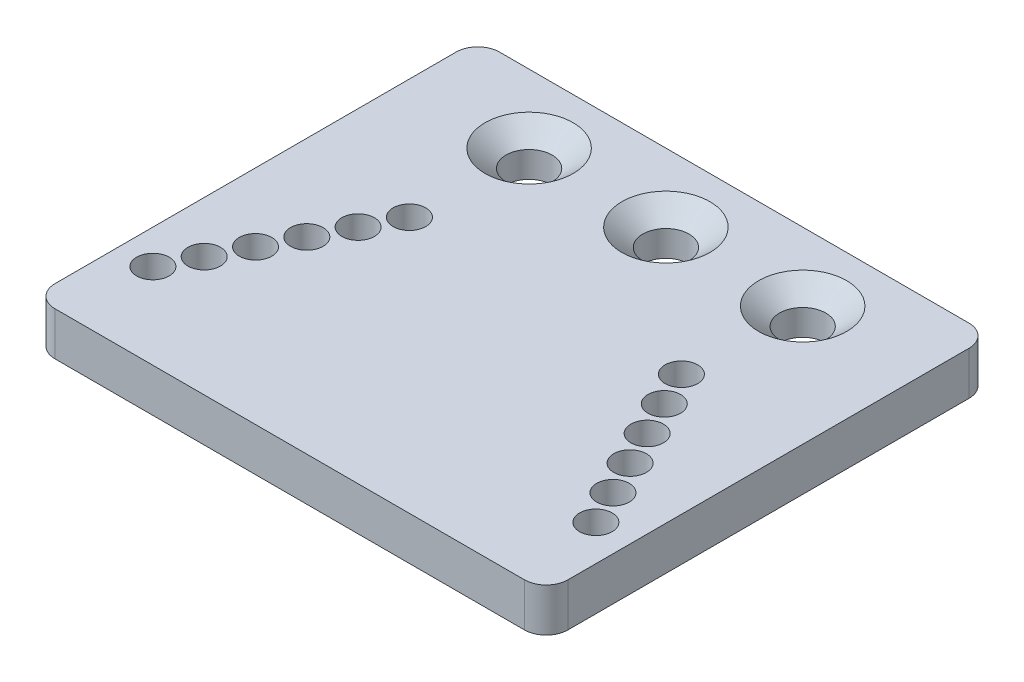
SolidWorks part; units mm, degrees
ref_plane "Front Plane" through (0, 0, 0) normal (0, 0, 1) x (1, 0, 0)
ref_plane "Top Plane" through (0, 0, 0) normal (0, 1, 0) x (1, 0, 0)
ref_plane "Right Plane" through (0, 0, 0) normal (1, 0, 0) x (0, 0, -1)
sketch "Sketch1" plane through (0, 0, 0) normal (0, 1, 0) x (1, 0, 0)
  line L1 (3.175, 0) -> (71.825, 0)
  line L2 (0, 3.175) -> (0, 61.825)
  line L3 (3.175, 65) -> (71.825, 65)
  line L4 (75, 3.175) -> (75, 61.825)
  line L5 (0, 0) -> (75, 65) construction
  line L6 (0, 65) -> (75, 0) construction
  arc A0 (75, 61.825) -> (71.825, 65) centre (71.825, 61.825) ccw
  arc A1 (75, 3.175) -> (71.825, 0) centre (71.825, 3.175) cw
  arc A2 (0, 3.175) -> (3.175, 0) centre (3.175, 3.175) ccw
  arc A3 (3.175, 65) -> (0, 61.825) centre (3.175, 61.825) ccw
  circle A4 centre (72.2625, 7.5) radius 2.3813 construction
  circle A5 centre (2.5, 7.5) radius 2.3813 construction
  circle A6 centre (5, 12.5) radius 2.3812
  circle A7 centre (69.7625, 12.5) radius 2.3813
  circle A8 centre (7.5, 17.5) radius 2.3813
  circle A9 centre (67.2625, 17.5) radius 2.3813
  circle A10 centre (10, 22.5) radius 2.3813
  circle A11 centre (64.7625, 22.5) radius 2.3813
  circle A12 centre (12.5, 27.5) radius 2.3813
  circle A13 centre (62.2625, 27.5) radius 2.3813
  circle A14 centre (15, 32.5) radius 2.3813
  circle A15 centre (59.7625, 32.5) radius 2.3812
  circle A16 centre (17.5, 37.5) radius 2.3813
  circle A17 centre (57.2625, 37.5) radius 2.3812
  circle A18 centre (37.5, 55) radius 3.3
  circle A19 centre (17.5, 55) radius 3.3
  circle A20 centre (57.5, 55) radius 3.3
  point P4 (37.5, 32.5)
  point P22 (69.8813, 7.5)
  point P23 (4.8813, 7.5)
  point P40 (9.8812, 17.5)
  point P41 (12.3812, 22.5)
  point P42 (14.8812, 27.5)
  point P43 (59.8812, 27.5)
  point P44 (7.3813, 12.5)
  point P45 (62.3813, 22.5)
  point P46 (64.8812, 17.5)
  point P47 (67.3813, 12.5)
  point P52 (17.3812, 32.5)
  point P53 (57.3812, 32.5)
  point P58 (54.8813, 37.5)
  point P60 (19.8812, 37.5)
  dimension "D3" = 3.175
  dimension "D4" = 65
  dimension "D5" = 4.7625
  dimension "D6" = 7.5
  dimension "D28" = 6.6
  dimension "D1" = 75
  dimension "D2" = 65
  dimension "D7" = 60
  dimension "D8" = 55
  dimension "D9" = 50
  dimension "D10" = 45
  dimension "D11" = 40
  dimension "D12" = 35
  dimension "D13" = 2.5
  dimension "D14" = 5
  dimension "D15" = 2.5
  dimension "D16" = 5
  dimension "D17" = 5
  dimension "D18" = 2.5
  dimension "D19" = 2.5
  dimension "D20" = 5
  dimension "D21" = 5
  dimension "D22" = 2.5
  dimension "D23" = 5
  dimension "D24" = 2.5
  dimension "D25" = 2.5
  dimension "D26" = 37.5
  dimension "D27" = 10
  dimension "D29" = 20
  dimension "D30" = 20
extrude "Boss-Extrude1" add sketch "Sketch1" along normal blind 6.35 contours L2 A3 L3 A0 L4 A1 L1 A2
hole_wizard "CSK for 1/4 Flat Head Machine Screw (100)1" positions "3DSketch1" profile "Sketch2" countersink size "1/4" standard "ANSI Inch" end condition up to next
sketch3d "3DSketch1"
  line L0 (17.5, 6.35, -55) -> (17.5, 0, -55) construction
  line L1 (57.5, 6.35, -55) -> (57.5, 0, -55) construction
  line L2 (37.5, 6.35, -55) -> (37.5, 0, -55) construction
  point P0 (17.5, 6.35, -55)
  point P4 (57.5, 6.35, -55)
  point P8 (37.5, 6.35, -55)
sketch "Sketch2" plane through (17.5, 6.35, -55) normal (1, 0, 0) x (0, 0, 1)
  line L0 (0, 0) -> (0, 6.35)
  line L1 (0, 6.35) -> (3.3782, 6.35)
  line L2 (3.3782, 6.35) -> (3.3782, 2.5682)
  line L3 (3.3782, 2.5682) -> (6.4389, 0)
  line L5 (6.4389, 0) -> (0, 0)
  line L6 (-3.3782, 2.5682) -> (-6.4389, 0) construction
  line L11 (0, -6.35) -> (0, 107.95) construction
  dimension "Thru Hole Dia." = 6.7564
  dimension "Thru Hole Depth" = 6.35
  dimension "Near C'Sink Dia." = 12.8778
  dimension "Near C'Sink Angle" = 100
